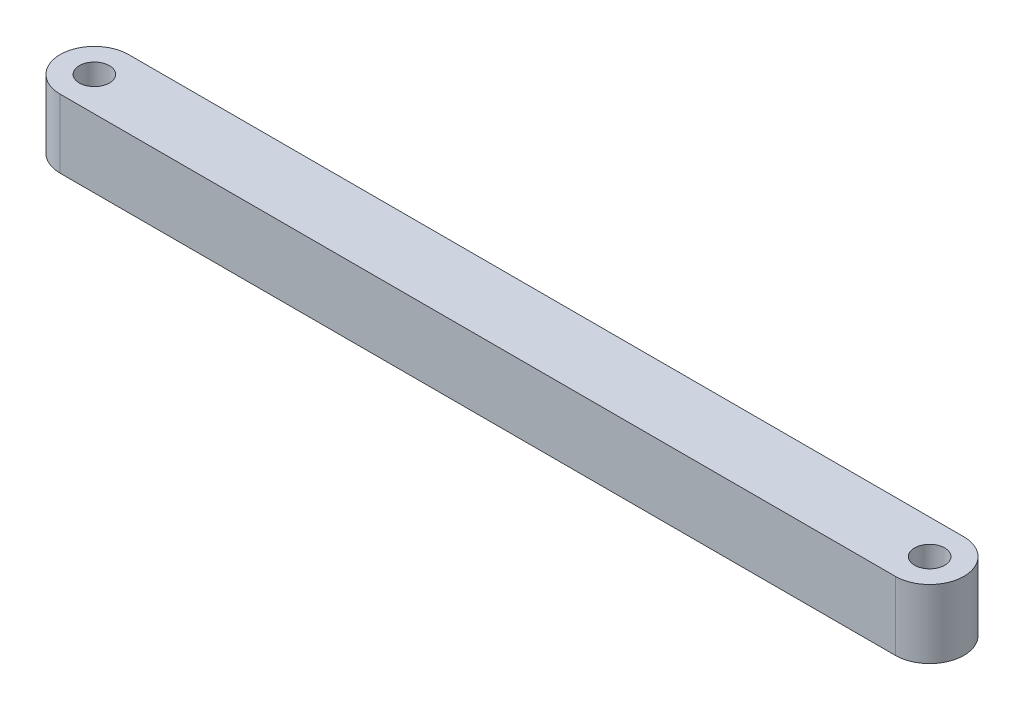
SolidWorks part; units mm, degrees
ref_plane "Front Plane" through (0, 0, 0) normal (0, 0, 1) x (1, 0, 0)
ref_plane "Top Plane" through (0, 0, 0) normal (0, 1, 0) x (1, 0, 0)
ref_plane "Right Plane" through (0, 0, 0) normal (1, 0, 0) x (0, 0, -1)
sketch "Sketch1" plane through (0, 0, 0) normal (0, 1, 0) x (1, 0, 0)
  line L0 (-58.7, 2.5) -> (2.2647, 2.5)
  line L1 (-58.7, -2.5) -> (2.2647, -2.5)
  arc A0 (-58.7, 2.5) -> (-58.7, -2.5) centre (-58.7, 0) ccw
  arc A1 (2.2647, -2.5) -> (2.2647, 2.5) centre (2.2647, 0) ccw
  circle A2 centre (2.2647, 0) radius 1.1
  circle A3 centre (-58.7, 0) radius 1.1
  point P4 (0, 0)
  dimension "D1" = 5
  dimension "D2" = 5
  dimension "D3" = 2.2
  dimension "D4" = 2.2
  dimension "D5" = 60.9647
extrude "Boss-Extrude1" add sketch "Sketch1" along normal blind 5
